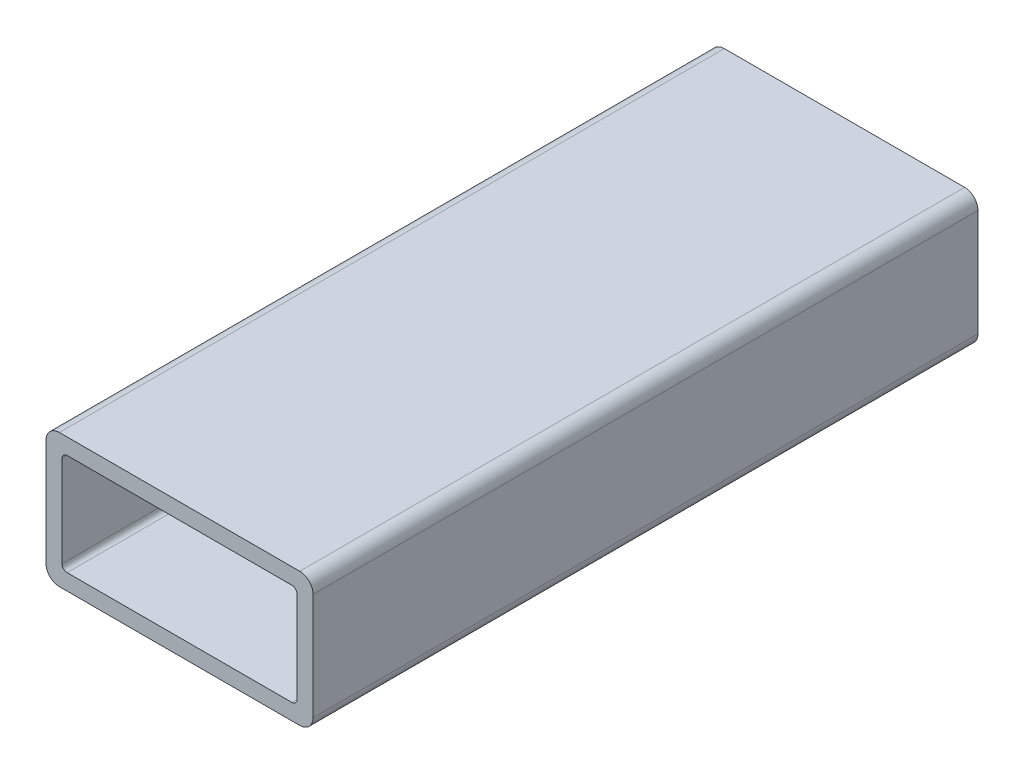
SolidWorks part; units mm, degrees
ref_plane "Front" through (0, 0, 0) normal (0, 0, 1) x (1, 0, 0)
ref_plane "Top" through (0, 0, 0) normal (0, 1, 0) x (1, 0, 0)
ref_plane "Right" through (0, 0, 0) normal (1, 0, 0) x (0, 0, -1)
sketch "Sketch1" plane through (0, 0, 0) normal (0, 0, 1) x (1, 0, 0)
  line L0 (-22.352, 0) -> (-25.4, 0) construction
  line L1 (22.86, -12.7) -> (-22.86, -12.7)
  line L2 (25.4, -10.16) -> (25.4, 10.16)
  line L3 (22.86, 12.7) -> (-22.86, 12.7)
  line L4 (-25.4, -10.16) -> (-25.4, 10.16)
  line L5 (25.4, -12.7) -> (-25.4, 12.7) construction
  line L6 (25.4, 12.7) -> (-25.4, -12.7) construction
  line L7 (21.3868, 9.652) -> (-21.3868, 9.652)
  line L8 (22.352, 8.6868) -> (22.352, -8.6868)
  line L9 (21.3868, -9.652) -> (-21.3868, -9.652)
  line L10 (-22.352, 8.6868) -> (-22.352, -8.6868)
  line L11 (22.352, 9.652) -> (-22.352, -9.652) construction
  line L12 (22.352, -9.652) -> (-22.352, 9.652) construction
  line L13 (0, -9.652) -> (0, -12.7) construction
  line L14 (22.352, -8.6868) -> (22.352, -12.7) construction
  line L16 (22.352, -12.7) -> (25.4, -12.7) construction
  arc A0 (-21.3868, -9.652) -> (-22.352, -8.6868) centre (-21.3868, -8.6868) cw
  arc A1 (22.352, -8.6868) -> (21.3868, -9.652) centre (21.3868, -8.6868) cw
  arc A2 (21.3868, 9.652) -> (22.352, 8.6868) centre (21.3868, 8.6868) cw
  arc A3 (-21.3868, 9.652) -> (-22.352, 8.6868) centre (-21.3868, 8.6868) ccw
  arc A4 (22.86, -12.7) -> (25.4, -10.16) centre (22.86, -10.16) ccw
  arc A5 (25.4, 10.16) -> (22.86, 12.7) centre (22.86, 10.16) ccw
  arc A6 (-22.86, 12.7) -> (-25.4, 10.16) centre (-22.86, 10.16) ccw
  arc A7 (-22.86, -12.7) -> (-25.4, -10.16) centre (-22.86, -10.16) cw
  point P0 (0, 0)
  point P6 (0, 0)
  dimension "D2" = 0.9652
  dimension "D3" = 2.54
sketch "Sketch2" plane through (0, 0, 0) normal (1, 0, 0) x (0, 0, -1)
  line L0 (-152.4, 0) -> (152.4, 0) construction
  dimension "Length" = 304.8
ref_plane "Plane1" through (25.4, 0, 0) normal (1, 0, 0) x (0, 0, -1)
sketch "Sketch5" plane through (25.4, 0, 0) normal (1, 0, 0) x (0, 0, -1)
  line L0 (-152.4, 12.7) -> (-152.4, -12.7) construction
  line L1 (152.4, 12.7) -> (152.4, -12.7) construction
sketch "Sketch4" plane through (0, 0, 0) normal (0, 0, 1) x (1, 0, 0)
  line L0 (25.4, -10.16) -> (25.4, 10.16) construction
  line L1 (22.86, 12.7) -> (-22.86, 12.7) construction
  line L2 (-25.4, -10.16) -> (-25.4, 10.16) construction
  line L3 (22.86, -12.7) -> (-22.86, -12.7) construction
  line L4 (22.352, 8.6868) -> (22.352, -8.6868) construction
  line L5 (21.3868, -9.652) -> (-21.3868, -9.652) construction
  line L6 (-22.352, 8.6868) -> (-22.352, -8.6868) construction
  line L7 (21.3868, 9.652) -> (-21.3868, 9.652) construction
  line L8 (25.4, -10.16) -> (25.4, 10.16)
  line L9 (22.86, 12.7) -> (-22.86, 12.7)
  line L10 (-25.4, -10.16) -> (-25.4, 10.16)
  line L11 (22.86, -12.7) -> (-22.86, -12.7)
  line L12 (22.352, 8.6868) -> (22.352, -8.6868)
  line L13 (21.3868, -9.652) -> (-21.3868, -9.652)
  line L14 (-22.352, 8.6868) -> (-22.352, -8.6868)
  line L15 (21.3868, 9.652) -> (-21.3868, 9.652)
  arc A0 (25.4, 10.16) -> (22.86, 12.7) centre (22.86, 10.16) ccw construction
  arc A1 (-22.86, 12.7) -> (-25.4, 10.16) centre (-22.86, 10.16) ccw construction
  arc A2 (-25.4, -10.16) -> (-22.86, -12.7) centre (-22.86, -10.16) ccw construction
  arc A3 (22.86, -12.7) -> (25.4, -10.16) centre (22.86, -10.16) ccw construction
  arc A4 (21.3868, -9.652) -> (22.352, -8.6868) centre (21.3868, -8.6868) ccw construction
  arc A5 (-22.352, -8.6868) -> (-21.3868, -9.652) centre (-21.3868, -8.6868) ccw construction
  arc A6 (-21.3868, 9.652) -> (-22.352, 8.6868) centre (-21.3868, 8.6868) ccw construction
  arc A7 (22.352, 8.6868) -> (21.3868, 9.652) centre (21.3868, 8.6868) ccw construction
  arc A8 (25.4, 10.16) -> (22.86, 12.7) centre (22.86, 10.16) ccw
  arc A9 (-22.86, 12.7) -> (-25.4, 10.16) centre (-22.86, 10.16) ccw
  arc A10 (-25.4, -10.16) -> (-22.86, -12.7) centre (-22.86, -10.16) ccw
  arc A11 (22.86, -12.7) -> (25.4, -10.16) centre (22.86, -10.16) ccw
  arc A12 (21.3868, -9.652) -> (22.352, -8.6868) centre (21.3868, -8.6868) ccw
  arc A13 (-22.352, -8.6868) -> (-21.3868, -9.652) centre (-21.3868, -8.6868) ccw
  arc A14 (-21.3868, 9.652) -> (-22.352, 8.6868) centre (-21.3868, 8.6868) ccw
  arc A15 (22.352, 8.6868) -> (21.3868, 9.652) centre (21.3868, 8.6868) ccw
extrude "Boss-Extrude1" add sketch "Sketch4" along normal blind 126.4818
equation "\"D3@Sketch1\"=\"Outside Width@Sketch1\"*.05"
equation "\"D2@Sketch1\"=\"D1@Sketch1\"*.05"
